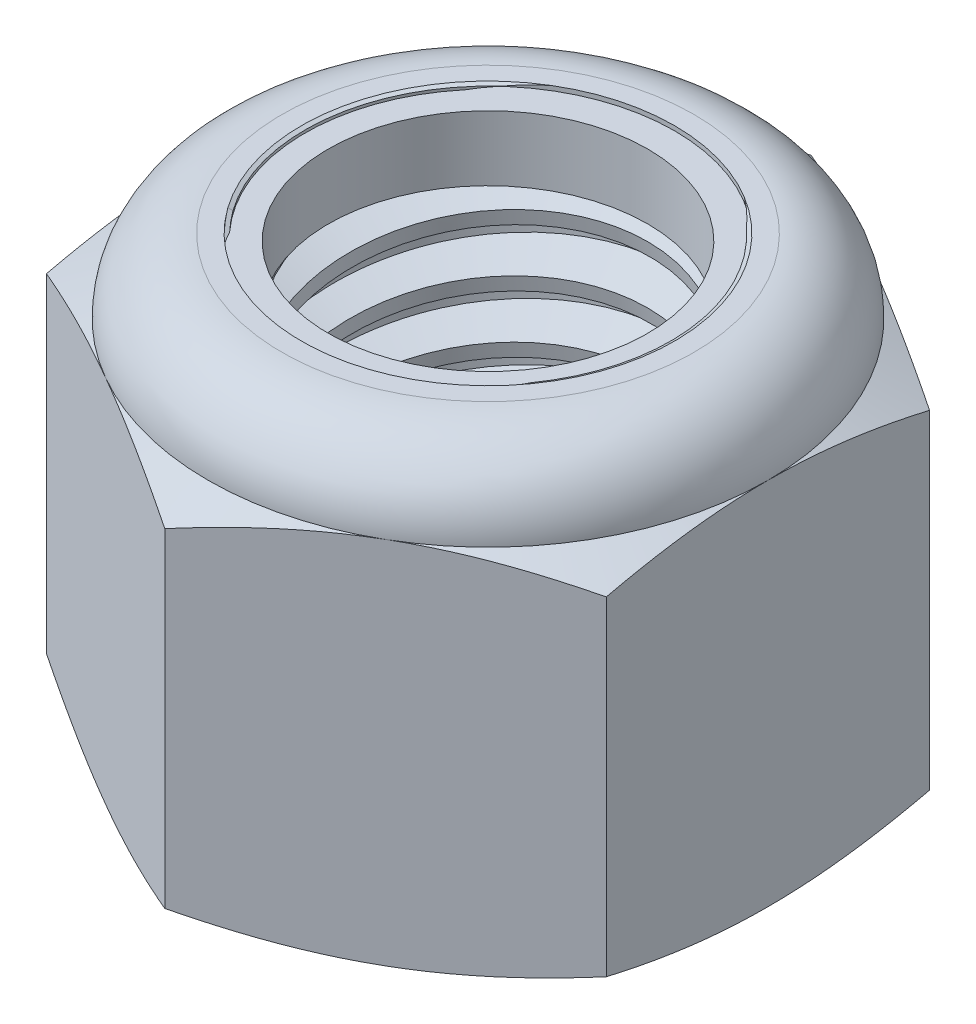
SolidWorks part; units mm, degrees
ref_plane "Front" through (0, 0, 0) normal (0, 0, 1) x (1, 0, 0)
ref_plane "Top" through (0, 0, 0) normal (0, 1, 0) x (1, 0, 0)
ref_plane "Right" through (0, 0, 0) normal (1, 0, 0) x (0, 0, -1)
sketch "Sketch1" plane through (0, 0, 0) normal (0, 1, 0) x (1, 0, 0)
  line L1 (0, 10.9985) -> (-9.525, 5.4993)
  line L2 (-9.525, 5.4993) -> (-9.525, -5.4993)
  line L3 (-9.525, -5.4993) -> (0, -10.9985)
  line L4 (0, -10.9985) -> (9.525, -5.4993)
  line L5 (9.525, -5.4993) -> (9.525, 5.4993)
  line L6 (9.525, 5.4993) -> (0, 10.9985)
  circle A0 centre (0, 0) radius 9.525 construction
  dimension "Hex Flats" = 19.05
extrude "Extrude1" add sketch "Sketch1" along normal blind 15.0812
sketch "Sketch2" plane through (0, 0, 0) normal (1, 0, 0) x (0, 0, -1)
  line L0 (-6.35, 0) -> (-6.35, 15.0812) construction
  line L1 (0, 0) -> (6.35, 0)
  line L2 (0, 0) -> (0, 15.0812)
  line L3 (0, 15.0812) -> (6.35, 15.0812)
  line L4 (6.35, 0) -> (6.35, 15.0812)
  line L5 (-5.4993, 15.0812) -> (5.4993, 15.0812) construction
  line L7 (0, -6.35) -> (0, 0) construction
  dimension "Thread Dia" = 12.7
revolve "Revolve1" add sketch "Sketch2" angle 360 about L7
sketch "Sketch3" plane through (0, 0, 0) normal (1, 0, 0) x (0, 0, -1)
  line L0 (6.35, 15.0813) -> (-6.35, 15.0812) construction
  line L1 (-6.35, 15.0812) -> (-6.35, 13.1274) construction
  line L2 (-6.35, 13.1274) -> (6.35, 15.0813) construction
  line L3 (6.35, 15.0813) -> (6.3871, 14.8399) construction
  line L4 (6.3871, 14.8399) -> (6.6471, 13.1501)
  line L5 (6.6471, 13.1501) -> (5.509, 13.5928)
  line L6 (5.509, 13.5928) -> (5.4347, 14.0756)
  line L7 (5.4347, 14.0756) -> (6.3871, 14.8399)
  line L8 (5.4719, 13.8342) -> (6.5171, 13.995) construction
  line L9 (6.35, 15.0813) -> (6.35, 13.9693) construction
  line L10 (6.35, 13.9693) -> (-6.35, 12.0154) construction
  line L11 (-6.35, 12.0154) -> (-6.35, 13.1274) construction
  line L12 (-0.3214, 15.0812) -> (0.3214, 10.9035) construction
  line L13 (-6.35, 0) -> (-6.35, 15.0812) construction
  line L14 (0, 15.0812) -> (6.35, 15.0812) construction
  line L15 (6.35, 0) -> (6.35, 15.0812) construction
  point P13 (0, 12.9924)
  dimension "D1" = 0.2442
  dimension "D2" = 0.4885
  dimension "Thread Pitch" = 1.9538
  dimension "D4" = 60
  dimension "D5" = 1.9538
revolve "Cut-Revolve1" cut sketch "Sketch3" angle 360 about L12
pattern_linear "LPattern1" count 8 spacing 1.9538 along (0, -1, 0) count 2 spacing 1.9538 along (0, 1, 0) of "Cut-Revolve1"
sketch "Sketch4" plane through (0, 0, 0) normal (1, 0, 0) x (0, 0, -1)
  line L0 (0, 15.0812) -> (6.35, 15.0812)
  line L1 (6.35, 15.0812) -> (5.4347, 14.6545)
  line L2 (5.4347, 14.6545) -> (5.4347, 0.4268)
  line L3 (5.4347, 0.4268) -> (6.35, 0)
  line L4 (6.35, 0) -> (0, 0)
  line L5 (0, 0) -> (0, 15.0812)
  line L6 (6.35, 0) -> (6.35, 15.0812) construction
  line L7 (0, 15.0812) -> (6.35, 15.0812) construction
  line L8 (0, 0) -> (6.35, 0) construction
  line L9 (0, 0) -> (0, 15.0812) construction
  line L10 (0, 15.0812) -> (0, 16.0911) construction
  dimension "D1" = 25
revolve "Cut-Revolve2" cut sketch "Sketch4" angle 360 about L10
combine bodies "Combine1" operation type subtract main body 112 bodies to subtract 111
sketch "Sketch5" plane through (0, 0, 0) normal (1, 0, 0) x (0, 0, -1)
  line L0 (0, 0) -> (9.525, 0)
  line L1 (9.525, 0) -> (10.9985, 0.6871)
  line L2 (10.9985, 0.6871) -> (10.9985, 11.8806)
  line L3 (10.9985, 11.8806) -> (9.525, 12.5677)
  line L4 (7.0115, 15.0813) -> (7.0115, 16.3513)
  line L5 (7.0115, 16.3513) -> (12.2685, 16.3513)
  line L6 (12.2685, 16.3513) -> (12.2685, -1.27)
  line L7 (12.2685, -1.27) -> (0, -1.27)
  line L8 (0, -1.27) -> (0, 0)
  line L9 (9.525, 12.5677) -> (9.525, 0) construction
  line L10 (0, 0) -> (6.35, 0) construction
  line L13 (10.9985, 6.2839) -> (12.2685, 6.2839) construction
  line L14 (10.9985, 15.0812) -> (10.9985, 0) construction
  line L15 (0, 0) -> (0, 16.3513) construction
  line L20 (0, 16.3513) -> (7.0115, 16.3513) construction
  line L22 (0, 15.0812) -> (6.35, 15.0812) construction
  arc A0 (9.525, 12.5677) -> (7.0115, 15.0813) centre (7.0115, 12.5677) ccw
  dimension "D1" = 25
  dimension "D2" = 1.27
  dimension "D3" = 15.0813
  dimension "D4" = 2.5135
revolve "Cut-Revolve3" cut sketch "Sketch5" angle 360 about L15
sketch "Sketch6" plane through (0, 0, 0) normal (1, 0, 0) x (0, 0, -1)
  line L0 (0, 12.5677) -> (9.3726, 12.5677)
  line L1 (7.0115, 14.9289) -> (6.2231, 14.9289)
  line L2 (0, 16.3513) -> (0, 12.5677)
  line L3 (6.2231, 16.3513) -> (0, 16.3513)
  line L4 (0, 16.3513) -> (7.0115, 16.3513) construction
  line L5 (0, 0) -> (0, 16.3513) construction
  line L6 (0, 16.3513) -> (0, 44.323) construction
  line L7 (6.2231, 14.9289) -> (6.2231, 16.3513)
  line L8 (7.0115, 15.0813) -> (7.0115, 14.9289) construction
  line L9 (6.2231, 14.9289) -> (5.4347, 14.9289) construction
  line L10 (5.4347, 14.9289) -> (5.4347, 14.6545) construction
  arc A0 (9.3726, 12.5677) -> (7.0115, 14.9289) centre (7.0115, 12.5677) ccw
  arc A1 (9.525, 12.5677) -> (7.0115, 15.0813) centre (7.0115, 12.5677) ccw construction
  dimension "D1" = 0.1524
revolve "Cut-Revolve4" cut sketch "Sketch6" angle 360 about L6
sketch "Sketch7" plane through (0, 0, 0) normal (1, 0, 0) x (0, 0, -1)
  line L0 (5.4347, 12.6439) -> (9.2951, 12.6439)
  line L1 (7.0115, 14.8527) -> (5.4347, 14.8527)
  line L2 (5.4347, 14.8527) -> (5.4347, 12.6439)
  line L3 (5.4347, 12.6439) -> (0, 12.6439) construction
  line L4 (0, 12.6439) -> (0, 14.8527) construction
  line L5 (0, 14.8527) -> (5.4347, 14.8527) construction
  line L6 (5.4347, 12.6439) -> (5.4347, 12.5677) construction
  line L7 (0, 12.5677) -> (9.3726, 12.5677) construction
  line L8 (7.0115, 14.8527) -> (7.0115, 14.9289) construction
  arc A0 (9.2951, 12.6439) -> (7.0115, 14.8527) centre (7.0115, 12.5677) ccw
  arc A2 (9.3726, 12.5677) -> (7.0115, 14.9289) centre (7.0115, 12.5677) ccw construction
  dimension "D1" = 0.0762
revolve "Revolve2" add sketch "Sketch7" angle 360 about L4
equation "\"D1@Sketch3\"=\"Thread Pitch@Sketch3\"/8"
equation "\"D2@Sketch3\"=\"Thread Pitch@Sketch3\"/4"
equation "\"D5@Sketch3\"=\"Thread Pitch@Sketch3\""
equation "\"D4@LPattern1\"=\"Thread Pitch@Sketch3\""
equation "\"D3@LPattern1\"=\"Thread Pitch@Sketch3\""
equation "\"D1@LPattern1\"=\"Height@Extrude1\"/\"Thread Pitch@Sketch3\""
equation "\"D4@Sketch5\"=\"Height@Extrude1\"/6"
